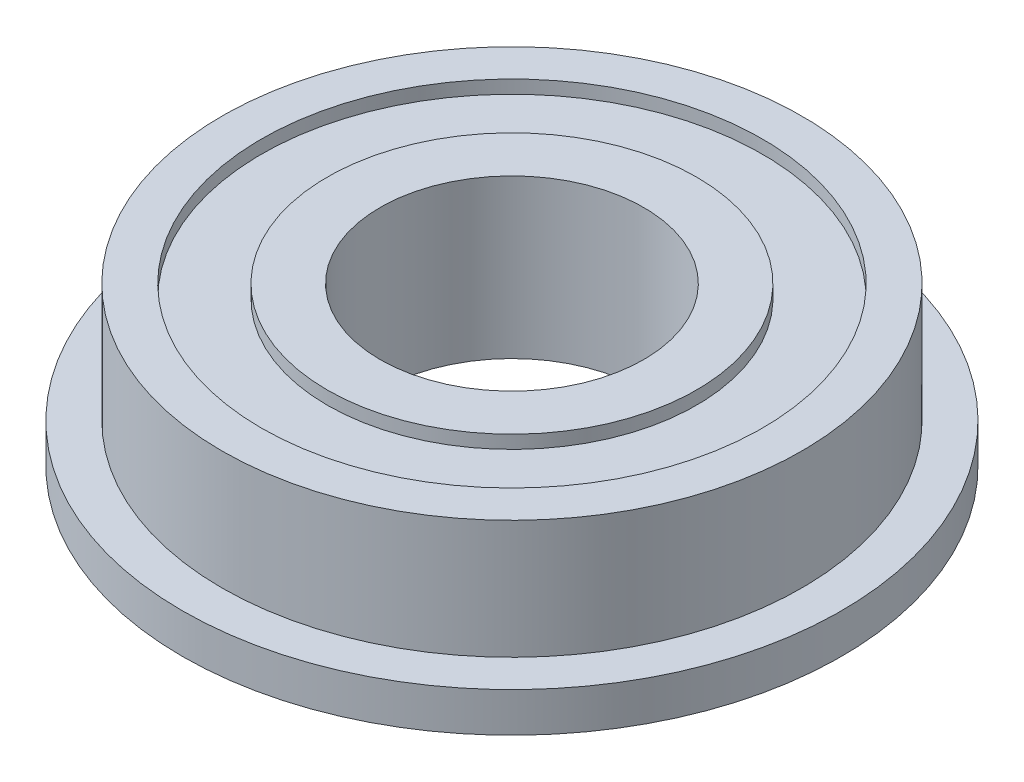
SolidWorks part; units mm, degrees
ref_plane "前视基准面" through (0, 0, 0) normal (0, 0, 1) x (1, 0, 0)
ref_plane "上视基准面" through (0, 0, 0) normal (0, 1, 0) x (1, 0, 0)
ref_plane "右视基准面" through (0, 0, 0) normal (1, 0, 0) x (0, 0, -1)
sketch "草图1" plane through (0, 0, 0) normal (0, 1, 0) x (1, 0, 0)
  circle A0 centre (0, 0) radius 12.5
  dimension "D1" = 25
extrude "凸台-拉伸1" add sketch "草图1" along normal blind 1.5
sketch "草图2" plane through (0, 1.5, 0) normal (0, 1, 0) x (1, 0, 0)
  circle A0 centre (0, 0) radius 11
  dimension "D1" = 22
extrude "凸台-拉伸2" add sketch "草图2" along normal blind 4.5
sketch "草图3" plane through (0, 6, 0) normal (0, 1, 0) x (1, 0, 0)
  circle A0 centre (0, 0) radius 5
  dimension "D1" = 10
extrude "切除-拉伸1" cut sketch "草图3" against normal blind 9
sketch "草图4" plane through (0, 0, 0) normal (0, -1, 0) x (1, 0, 0)
  circle A0 centre (0, 0) radius 7
  circle A1 centre (0, 0) radius 9.5
  dimension "14" = 14
  dimension "D2" = 19
extrude "切除-拉伸2" cut sketch "草图4" against normal blind 0.5
sketch "草图5" plane through (0, 6, 0) normal (0, 1, 0) x (1, 0, 0)
  circle A0 centre (0, 0) radius 7
  circle A1 centre (0, 0) radius 9.5
  dimension "D1" = 14
  dimension "D2" = 19
extrude "切除-拉伸3" cut sketch "草图5" against normal blind 0.5
